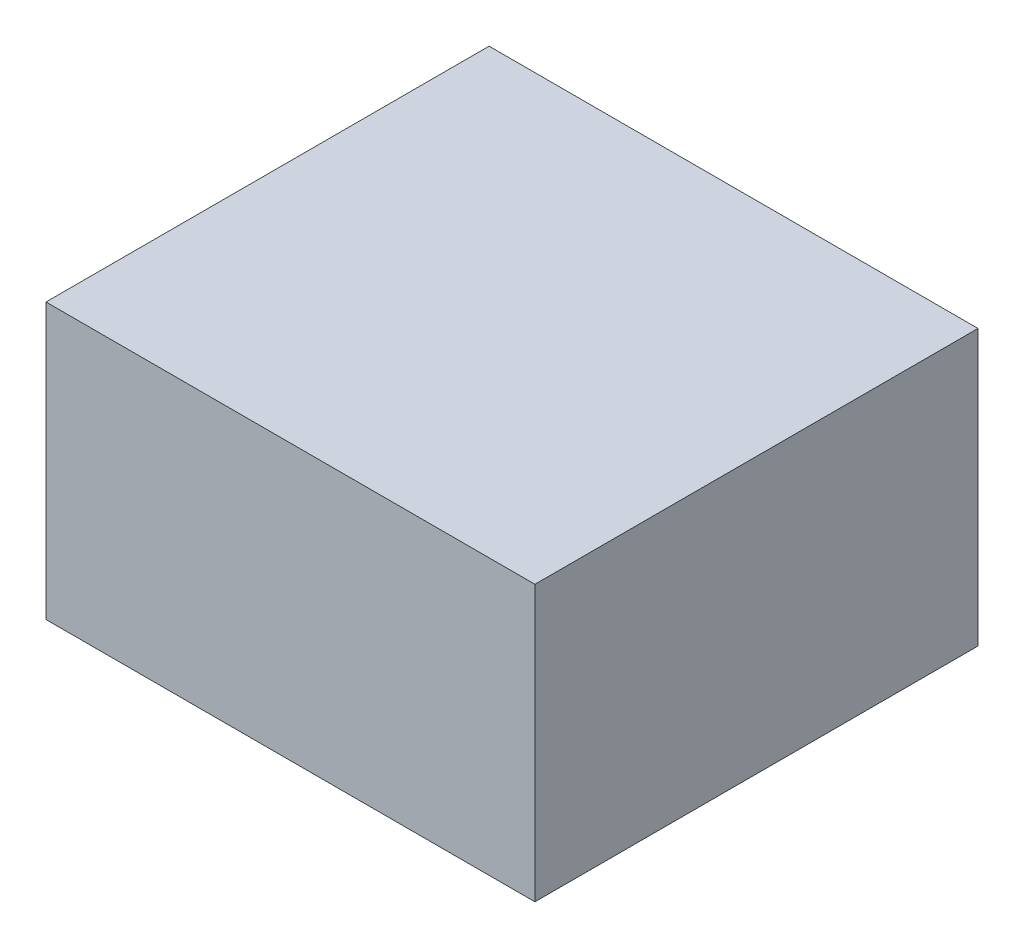
SolidWorks part; units mm, degrees
ref_plane "Front Plane" through (0, 0, 0) normal (0, 0, 1) x (1, 0, 0)
ref_plane "Top Plane" through (0, 0, 0) normal (0, 1, 0) x (1, 0, 0)
ref_plane "Right Plane" through (0, 0, 0) normal (1, 0, 0) x (0, 0, -1)
sketch "Sketch1" plane through (0, 0, 0) normal (0, 1, 0) x (1, 0, 0)
  line L1 (-50.8, 46.0375) -> (50.8, 46.0375)
  line L2 (-50.8, 46.0375) -> (-50.8, -46.0375)
  line L3 (-50.8, -46.0375) -> (50.8, -46.0375)
  line L4 (50.8, 46.0375) -> (50.8, -46.0375)
  line L5 (-50.8, 46.0375) -> (50.8, -46.0375) construction
  line L6 (-50.8, -46.0375) -> (50.8, 46.0375) construction
  point P0 (0, 0)
  dimension "D1" = 92.075
  dimension "D2" = 101.6
extrude "Boss-Extrude1" add sketch "Sketch1" along normal blind 57.15
